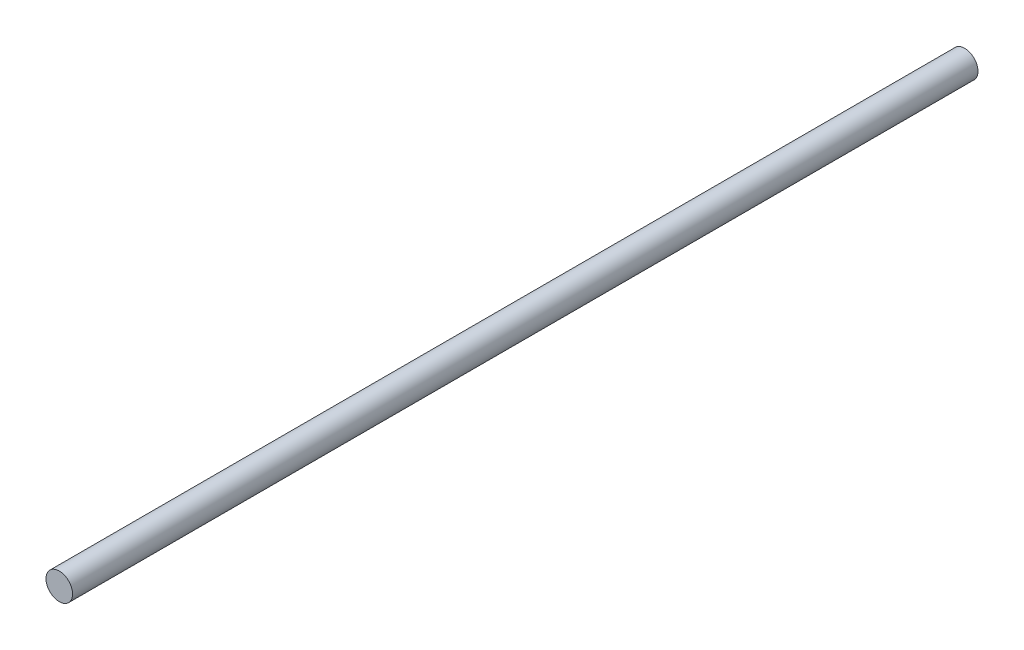
SolidWorks part; units mm, degrees
material "Thornel Mat VMA"
ref_plane "Front Plane" through (0, 0, 0) normal (0, 0, 1) x (1, 0, 0)
ref_plane "Top Plane" through (0, 0, 0) normal (0, 1, 0) x (1, 0, 0)
ref_plane "Right Plane" through (0, 0, 0) normal (1, 0, 0) x (0, 0, -1)
sketch "Sketch1" plane through (0, 0, 0) normal (0, 0, 1) x (1, 0, 0)
  circle A0 centre (0, 0) radius 6.35
  dimension "D1" = 12.7
extrude "Boss-Extrude1" add sketch "Sketch1" along normal blind 432.562
